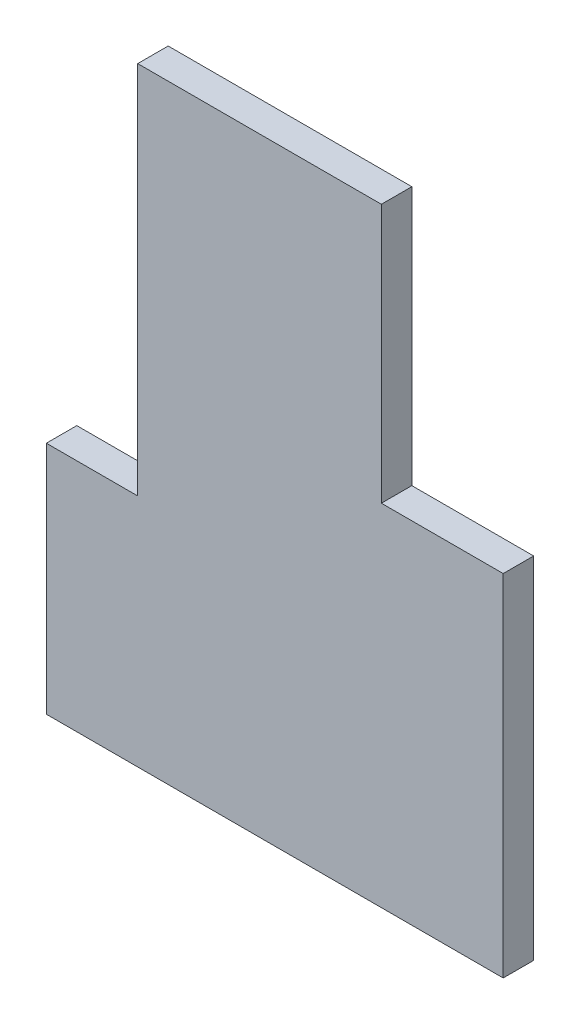
SolidWorks part; units mm, degrees
ref_plane "Front Plane" through (0, 0, 0) normal (0, 0, 1) x (1, 0, 0)
ref_plane "Top Plane" through (0, 0, 0) normal (0, 1, 0) x (1, 0, 0)
ref_plane "Right Plane" through (0, 0, 0) normal (1, 0, 0) x (0, 0, -1)
sketch "Sketch2" plane through (0, 0, 0) normal (0, 0, 1) x (1, 0, 0)
  line L0 (-35.4557, -20.7343) -> (114.5443, -20.7343)
  line L1 (114.5443, -20.7343) -> (114.5443, 94.2657)
  line L2 (74.5443, 179.2657) -> (-5.4557, 179.2657)
  line L3 (-35.4557, 56.3295) -> (-35.4557, -20.7343)
  line L4 (114.5443, 94.2657) -> (74.5443, 94.2657)
  line L5 (74.5443, 94.2657) -> (74.5443, 179.2657)
  line L6 (-35.4557, 56.3295) -> (-5.4557, 56.3295)
  line L7 (-5.4557, 56.3295) -> (-5.4557, 179.2657)
  dimension "D1" = 30
  dimension "D2" = 40
  dimension "D3" = 150
  dimension "D4" = 200
extrude "Boss-Extrude1" add sketch "Sketch2" along normal blind 10
